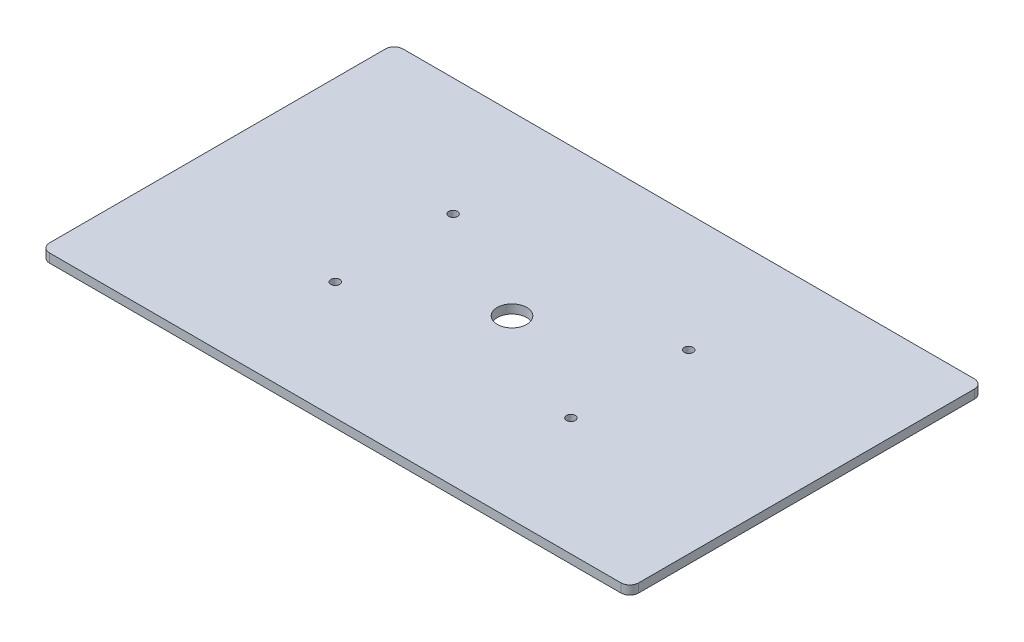
SolidWorks part; units mm, degrees
ref_plane "Front Plane" through (0, 0, 0) normal (0, 0, 1) x (1, 0, 0)
ref_plane "Top Plane" through (0, 0, 0) normal (0, 1, 0) x (1, 0, 0)
ref_plane "Right Plane" through (0, 0, 0) normal (1, 0, 0) x (0, 0, -1)
sketch "Sketch1" plane through (0, 0, 0) normal (0, 1, 0) x (1, 0, 0)
  line L1 (-100, 60) -> (100, 60)
  line L2 (-100, 60) -> (-100, -60)
  line L3 (-100, -60) -> (100, -60)
  line L4 (100, 60) -> (100, -60)
  line L5 (-100, 60) -> (100, -60) construction
  line L6 (-100, -60) -> (100, 60) construction
  point P0 (0, 0)
extrude "Boss-Extrude1" add sketch "Sketch1" along normal blind 3
fillet "Fillet1" radius 3 4 edges at (-100, 1.5, -60) (-100, 1.5, 60) (100, 1.5, -60) (100, 1.5, 60)
sketch "Sketch2" plane through (0, 3, 0) normal (0, 1, 0) x (1, 0, 0)
  circle A0 centre (40, 20) radius 1.5
  dimension "D1" = 40
  dimension "D2" = 20
extrude "Cut-Extrude1" cut sketch "Sketch2" against normal blind 3
mirror "Mirror1" about plane through (0, 0, 0) normal (0, 0, 1) of "Cut-Extrude1"
mirror "Mirror2" about plane through (0, 0, 0) normal (1, 0, 0) of "Mirror1", "Cut-Extrude1"
sketch "Sketch3" plane through (0, 3, 0) normal (0, 1, 0) x (1, 0, 0)
  circle A0 centre (0, 0) radius 5
extrude "Cut-Extrude2" cut sketch "Sketch3" against normal blind 3
